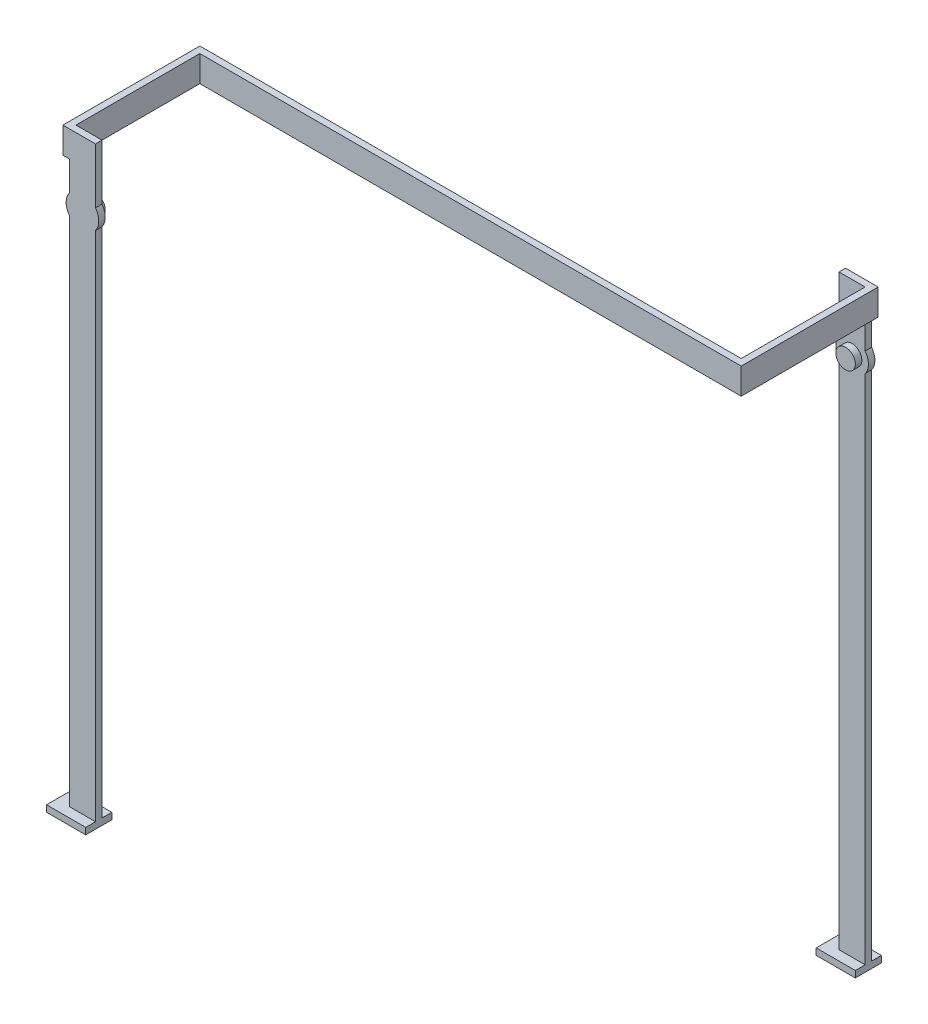
SolidWorks part; units mm, degrees
ref_plane "前视基准面" through (0, 0, 0) normal (0, 0, 1) x (1, 0, 0)
ref_plane "上视基准面" through (0, 0, 0) normal (0, 1, 0) x (1, 0, 0)
ref_plane "右视基准面" through (0, 0, 0) normal (1, 0, 0) x (0, 0, -1)
sketch "草图1" plane through (0, 0, -19.5) normal (0, 0, -1) x (-1, 0, 0)
  line L0 (-21.7223, 40.0928) -> (-21.7223, -38.4072)
  line L1 (-25.7223, 51.5928) -> (-21.7223, 51.5928)
  line L2 (-25.7223, 51.5928) -> (-25.7223, 43.0928)
  line L3 (-25.7223, -38.4072) -> (-21.7223, -38.4072)
  line L4 (-21.7223, 51.5928) -> (-21.7223, 43.0928)
  line L5 (-25.7223, 40.0928) -> (-25.7223, -38.4072)
  arc A0 (-25.7223, 43.0928) -> (-25.7223, 40.0928) centre (-23.7223, 41.5928) ccw
  arc A1 (-21.7223, 40.0928) -> (-21.7223, 43.0928) centre (-23.7223, 41.5928) ccw
  point P0 (-23.7223, 41.5928)
  dimension "D1" = 80
  dimension "D2" = 4
  dimension "D3" = 10
extrude "凸台-拉伸1" add sketch "草图1" along normal blind 1
sketch "草图2" plane through (0, 0, -19.5) normal (0, 0, 1) x (1, 0, 0)
  circle A0 centre (23.7223, 41.5928) radius 1.5
extrude "凸台-拉伸2" add sketch "草图2" along normal blind 1
sketch "草图3" plane through (0, 0, 19.5) normal (0, 0, 1) x (1, 0, 0)
  line L0 (-52.2777, 40.0928) -> (-52.2777, -38.4072)
  line L1 (-56.2777, 51.5928) -> (-52.2777, 51.5928)
  line L2 (-56.2777, 51.5928) -> (-56.2777, 43.0928)
  line L3 (-56.2777, -38.4072) -> (-52.2777, -38.4072)
  line L4 (-52.2777, 51.5928) -> (-52.2777, 43.0928)
  line L5 (-56.2777, 40.0928) -> (-56.2777, -38.4072)
  arc A0 (-56.2777, 43.0928) -> (-56.2777, 40.0928) centre (-54.2777, 41.5928) ccw
  arc A1 (-52.2777, 40.0928) -> (-52.2777, 43.0928) centre (-54.2777, 41.5928) ccw
  point P0 (-54.2777, 41.5928)
  dimension "D1" = 4
  dimension "D2" = 80
  dimension "D3" = 10
extrude "凸台-拉伸3" add sketch "草图3" along normal blind 1 separate body
sketch "草图4" plane through (0, 0, 19.5) normal (0, 0, -1) x (-1, 0, 0)
  circle A0 centre (54.2777, 41.5928) radius 1.5
  point P0 (54.2777, 41.5928)
extrude "凸台-拉伸5" add sketch "草图4" along normal blind 1
sketch "草图5" plane through (0, 0, 0) normal (0, 0, 1) x (1, 0, 0)
  line L0 (25.7223, 51.5928) -> (25.7223, 43.0928) construction
  line L1 (-56.2777, 51.5928) -> (25.7223, 51.5928)
  line L2 (-56.2777, 51.5928) -> (-56.2777, 47.5928)
  line L3 (-56.2777, 47.5928) -> (25.7223, 47.5928)
  line L4 (25.7223, 51.5928) -> (25.7223, 47.5928)
  dimension "D1" = 4
extrude "凸台-拉伸6" add sketch "草图5" along normal mid plane 1 separate body
sketch "草图6" plane through (-56.2777, 0, 0) normal (-1, 0, 0) x (0, 0, 1)
  line L1 (20.5, 51.5928) -> (-0.5, 51.5928)
  line L2 (20.5, 51.5928) -> (20.5, 47.5928)
  line L3 (20.5, 47.5928) -> (-0.5, 47.5928)
  line L4 (-0.5, 51.5928) -> (-0.5, 47.5928)
extrude "凸台-拉伸7" add sketch "草图6" along normal blind 1
sketch "草图7" plane through (25.7223, 0, 0) normal (1, 0, 0) x (0, 0, -1)
  line L1 (20.5, 51.5928) -> (-0.5, 51.5928)
  line L2 (20.5, 51.5928) -> (20.5, 47.5928)
  line L3 (20.5, 47.5928) -> (-0.5, 47.5928)
  line L4 (-0.5, 51.5928) -> (-0.5, 47.5928)
extrude "凸台-拉伸8" add sketch "草图7" along normal blind 1
sketch "草图8" plane through (0, -38.4072, 0) normal (0, -1, 0) x (1, 0, 0)
  line L0 (-52.2777, 20.5) -> (-52.2777, 19.5) construction
  line L1 (-58.2777, 22) -> (-52.2777, 22)
  line L2 (-58.2777, 22) -> (-58.2777, 18)
  line L3 (-58.2777, 18) -> (-52.2777, 18)
  line L4 (-52.2777, 22) -> (-52.2777, 18)
  line L5 (-56.2777, 20.5) -> (-52.2777, 20.5) construction
  line L6 (-56.2777, 19.5) -> (-52.2777, 19.5) construction
  line L7 (-56.2777, 20.5) -> (-56.2777, 19.5) construction
  line L8 (25.7223, -20.5) -> (25.7223, -19.5) construction
  line L9 (25.7223, -22) -> (19.7223, -22)
  line L10 (25.7223, -22) -> (25.7223, -18)
  line L11 (25.7223, -18) -> (19.7223, -18)
  line L12 (19.7223, -22) -> (19.7223, -18)
  line L13 (25.7223, -20.5) -> (21.7223, -20.5) construction
  line L14 (25.7223, -19.5) -> (21.7223, -19.5) construction
  line L15 (21.7223, -20.5) -> (21.7223, -19.5) construction
  dimension "D1" = 0
  dimension "D2" = 1.5
  dimension "D3" = 1.5
  dimension "D4" = 2
  dimension "D5" = 0
  dimension "D6" = 1.5
  dimension "D7" = 1.5
  dimension "D8" = 2
extrude "凸台-拉伸9" add sketch "草图8" along normal blind 1
